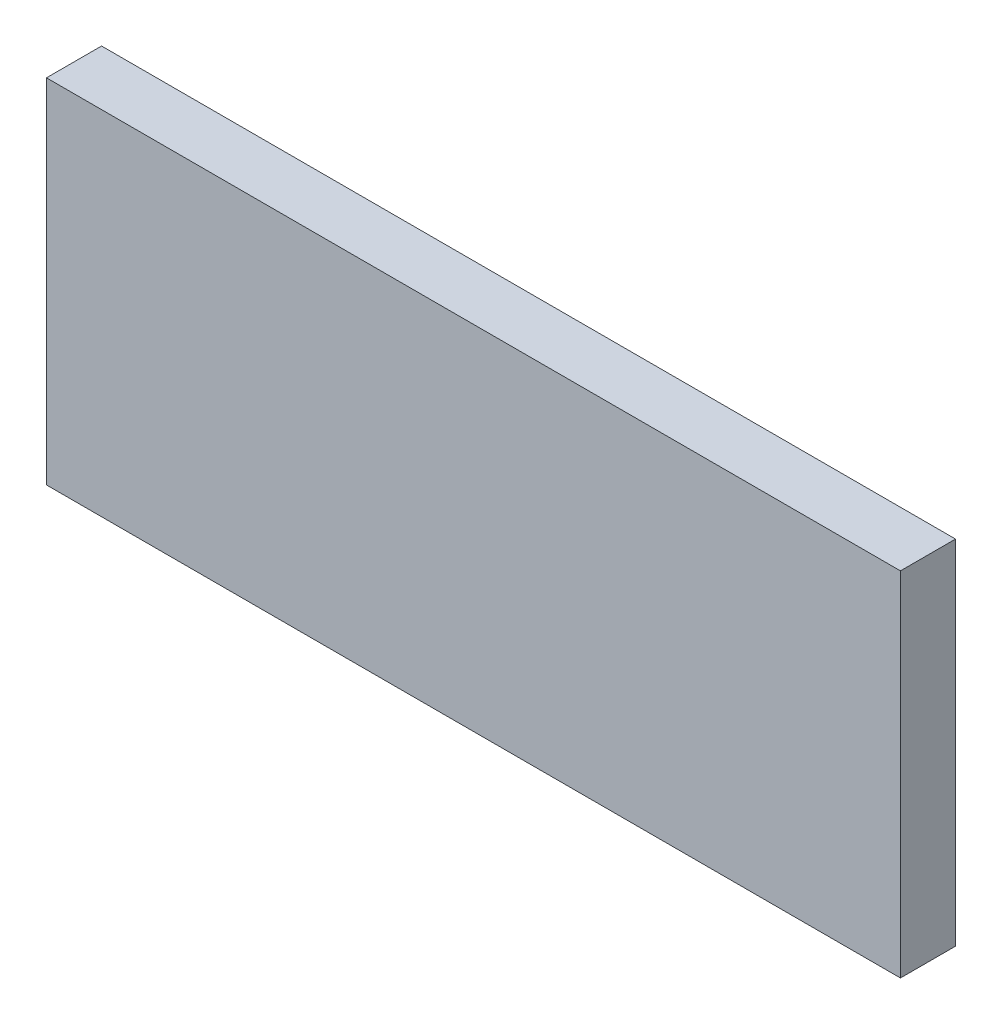
SolidWorks part; units mm, degrees
ref_plane "Plan de face" through (0, 0, 0) normal (0, 0, 1) x (1, 0, 0)
ref_plane "Plan de dessus" through (0, 0, 0) normal (0, 1, 0) x (1, 0, 0)
ref_plane "Plan de droite" through (0, 0, 0) normal (1, 0, 0) x (0, 0, -1)
sketch "Esquisse1" plane through (0, 0, 0) normal (0, 0, 1) x (1, 0, 0)
  line L1 (0, 0) -> (-155, 0)
  line L2 (0, 0) -> (0, 64)
  line L3 (0, 64) -> (-155, 64)
  line L4 (-155, 0) -> (-155, 64)
  dimension "D1" = 155
  dimension "D2" = 64
extrude "Boss.-Extru.1" add sketch "Esquisse1" along normal blind 10
